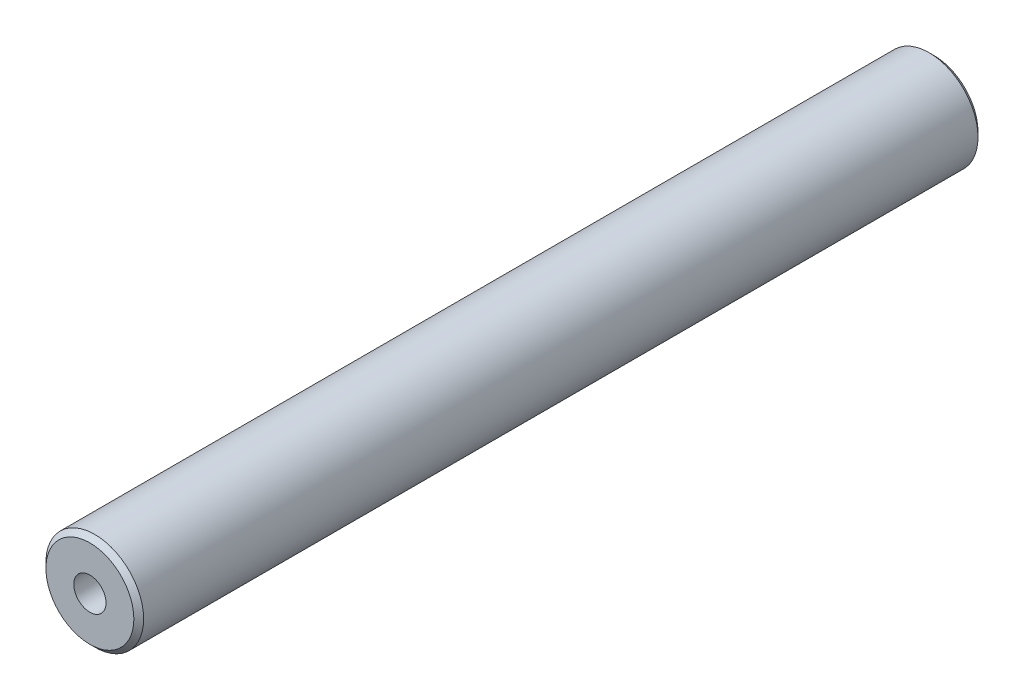
SolidWorks part; units mm, degrees
ref_plane "Plan de face" through (0, 0, 0) normal (0, 0, 1) x (1, 0, 0)
ref_plane "Plan de dessus" through (0, 0, 0) normal (0, 1, 0) x (1, 0, 0)
ref_plane "Plan de droite" through (0, 0, 0) normal (1, 0, 0) x (0, 0, -1)
sketch "Esquisse1" plane through (0, 0, 0) normal (0, 0, 1) x (1, 0, 0)
  circle A0 centre (0, 0) radius 5
extrude "Boss.-Extru.1" add sketch "Esquisse1" along normal blind 86.4
hole_wizard "Trou taraudé M4x0.71" positions "Esquisse2" profile "Esquisse3" tap size "M4x0.7" standard "Ansi Metric"
sketch "Esquisse2" plane through (0, 0, 86.4) normal (0, 0, 1) x (1, 0, 0)
  point P0 (0, 0)
sketch "Esquisse3" plane through (0, 0, 86.4) normal (1, 0, 0) x (0, -1, 0)
  line L0 (0, 0) -> (0, 20.9914)
  line L1 (0, 20.9914) -> (1.65, 20)
  line L2 (1.65, 20) -> (1.65, 0)
  line L5 (1.65, 0) -> (0, 0)
  line L10 (0, 20.9914) -> (-1.65, 20) construction
  line L11 (0, -6.35) -> (0, 107.95) construction
  dimension "Diamètre du trou pour taraudage" = 3.3
  dimension "Profondeur du trou pour taraudage" = 20
  dimension "Angle de pointe" = 118
cosmetic thread "Filetage de perçage1" parameters "D1"=8, "D2"=4
hole_wizard "Trou taraudé M4x0.72" positions "Esquisse4" profile "Esquisse5" tap size "M4x0.7" standard "Ansi Metric"
sketch "Esquisse4" plane through (0, 0, 0) normal (0, 0, -1) x (-1, 0, 0)
  point P0 (0, 0)
sketch "Esquisse5" plane through (0, 0, 0) normal (1, 0, 0) x (0, 1, 0)
  line L0 (0, 0) -> (0, 20.9914)
  line L1 (0, 20.9914) -> (1.65, 20)
  line L2 (1.65, 20) -> (1.65, 0)
  line L5 (1.65, 0) -> (0, 0)
  line L10 (0, 20.9914) -> (-1.65, 20) construction
  line L11 (0, -6.35) -> (0, 107.95) construction
  dimension "Diamètre du trou pour taraudage" = 3.3
  dimension "Profondeur du trou pour taraudage" = 20
  dimension "Angle de pointe" = 118
cosmetic thread "Filetage de perçage2" parameters "D1"=8, "D2"=4
chamfer "Chanfrein1" distance 0.5 angle 45 2 edges at (5, 0, 86.4) (5, 0, 0)
